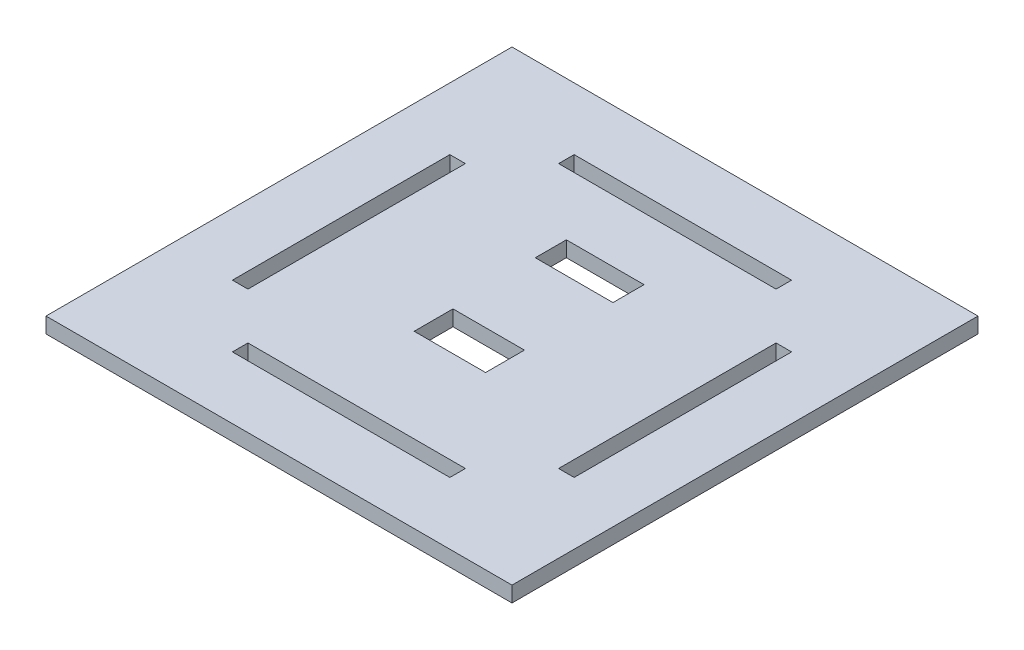
SolidWorks part; units mm, degrees
ref_plane "Front Plane" through (0, 0, 0) normal (0, 0, 1) x (1, 0, 0)
ref_plane "Top Plane" through (0, 0, 0) normal (0, 1, 0) x (1, 0, 0)
ref_plane "Right Plane" through (0, 0, 0) normal (1, 0, 0) x (0, 0, -1)
sketch "Sketch1" plane through (0, 0, 0) normal (0, 1, 0) x (1, 0, 0)
  line L1 (0, 0) -> (-150, 0)
  line L2 (0, 0) -> (0, 150)
  line L3 (0, 150) -> (-150, 150)
  line L4 (-150, 0) -> (-150, 150)
  line L9 (-110, 130) -> (-40, 130)
  line L10 (-110, 130) -> (-110, 125)
  line L11 (-110, 125) -> (-40, 125)
  line L12 (-40, 130) -> (-40, 125)
  line L13 (-20, 110) -> (-25, 110)
  line L14 (-20, 110) -> (-20, 40)
  line L15 (-20, 40) -> (-25, 40)
  line L16 (-25, 110) -> (-25, 40)
  line L21 (-125, 110) -> (-130, 110)
  line L22 (-125, 110) -> (-125, 40)
  line L23 (-125, 40) -> (-130, 40)
  line L24 (-130, 110) -> (-130, 40)
  line L29 (-110, 20) -> (-40, 20)
  line L30 (-110, 20) -> (-110, 25)
  line L31 (-110, 25) -> (-40, 25)
  line L32 (-40, 20) -> (-40, 25)
  line L33 (-86.5, 67.5) -> (-63.5, 67.5)
  line L34 (-86.5, 67.5) -> (-86.5, 55)
  line L35 (-86.5, 55) -> (-63.5, 55)
  line L36 (-63.5, 67.5) -> (-63.5, 55)
  line L37 (-87.5, 105) -> (-62.5, 105)
  line L38 (-87.5, 105) -> (-87.5, 95)
  line L39 (-87.5, 95) -> (-62.5, 95)
  line L40 (-62.5, 105) -> (-62.5, 95)
  point P5 (-22.5, 40)
  dimension "D1" = 150
  dimension "D2" = 150
  dimension "D3" = 70
  dimension "D4" = 70
  dimension "D5" = 70
  dimension "D6" = 70
  dimension "D7" = 5
  dimension "D8" = 5
  dimension "D9" = 5
  dimension "D10" = 5
  dimension "D11" = 40
  dimension "D12" = 40
  dimension "D13" = 40
  dimension "D14" = 40
  dimension "D15" = 20
  dimension "D16" = 20
  dimension "D17" = 20
  dimension "D18" = 20
  dimension "D19" = 23
  dimension "D20" = 12.5
  dimension "D21" = 30
  dimension "D22" = 38.5
  dimension "D23" = 25
  dimension "D24" = 10
  dimension "D25" = 37.5
  dimension "D26" = 20
extrude "Boss-Extrude1" add sketch "Sketch1" along normal blind 5
